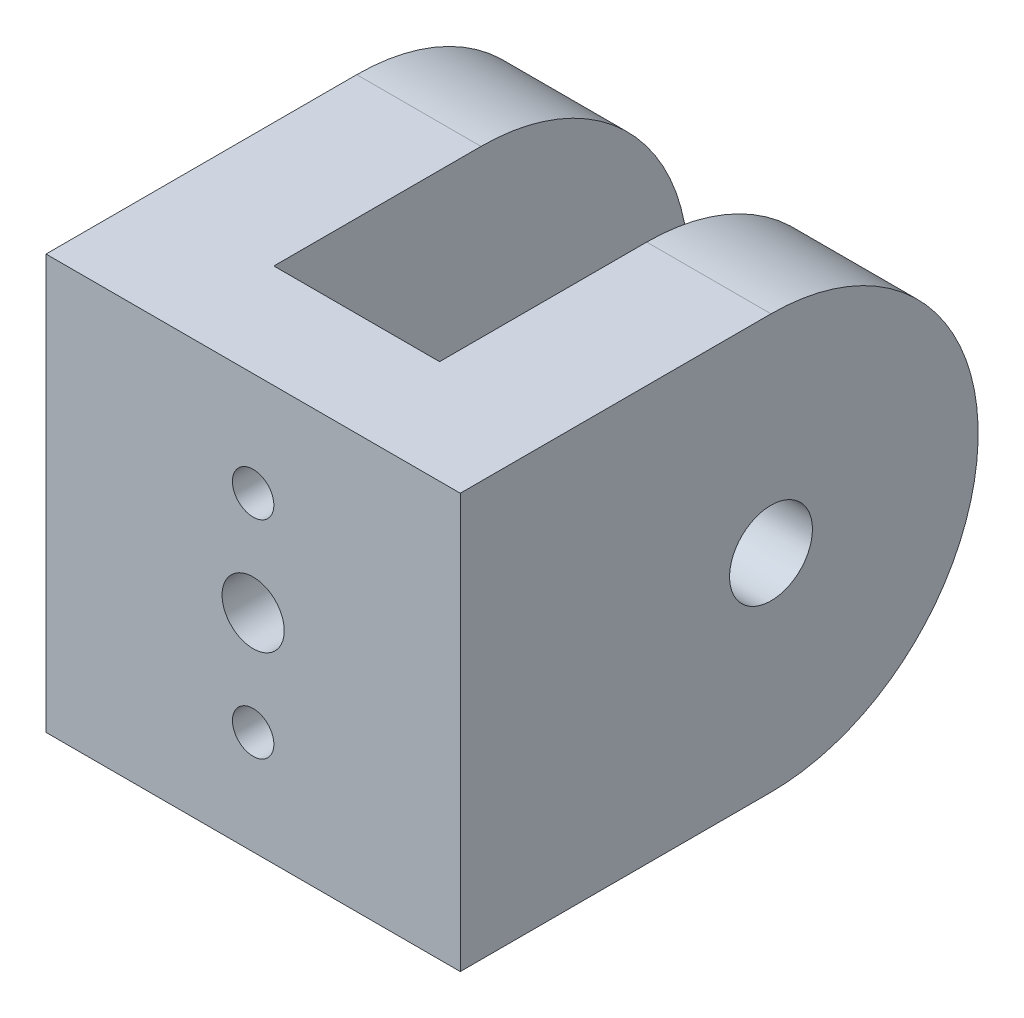
SolidWorks part; units mm, degrees
ref_plane "Front" through (0, 0, 0) normal (0, 0, 1) x (1, 0, 0)
ref_plane "Top" through (0, 0, 0) normal (0, 1, 0) x (1, 0, 0)
ref_plane "Right" through (0, 0, 0) normal (1, 0, 0) x (0, 0, -1)
sketch "Sketch1" plane through (0, 0, 0) normal (0, 0, 1) x (1, 0, 0)
  line L1 (0, 0) -> (80, 0)
  line L2 (0, 0) -> (0, 80)
  line L3 (0, 80) -> (80, 80)
  line L4 (80, 0) -> (80, 80)
  dimension "D1" = 80
  dimension "D2" = 80
extrude "Boss-Extrude1" add sketch "Sketch1" along normal blind 2
sketch "Sketch2" plane through (0, 0, 2) normal (0, 0, 1) x (1, 0, 0)
  line L0 (1, 79) -> (1, 1)
  line L1 (0, 80) -> (80, 80)
  line L2 (0, 80) -> (0, 0)
  line L3 (0, 0) -> (80, 0)
  line L4 (80, 80) -> (80, 0)
  line L5 (1, 1) -> (79, 1)
  line L6 (79, 79) -> (79, 1)
  line L7 (1, 79) -> (79, 79)
  dimension "D1" = 1
extrude "Boss-Extrude2" add sketch "Sketch2" along normal blind 15
fillet "Fillet1" radius 20 4 edges at (79, 1, 9.5) (1, 1, 9.5) (79, 79, 9.5) (1, 79, 9.5)
fillet "Fillet2" radius 10 8 edges at (73.1421, 73.1421, 2) (79, 40, 2) (73.1421, 6.8579, 2) (40, 1, 2) (6.8579, 6.8579, 2) (1, 40, 2) (6.8579, 73.1421, 2) (40, 79, 2)
fillet "Fillet3" radius 20 4 edges at (80, 0, 8.5) (80, 80, 8.5) (0, 80, 8.5) (0, 0, 8.5)
fillet "Fillet4" radius 10 8 edges at (5.8579, 5.8579, 0) (0, 40, 0) (5.8579, 74.1421, 0) (40, 80, 0) (74.1421, 74.1421, 0) (80, 40, 0) (74.1421, 5.8579, 0) (40, 0, 0)
sketch "Sketch3" plane through (0, 0, 17) normal (0, 0, 1) x (1, 0, 0)
  line L0 (72.2928, 5.3721) -> (70.635, 4.1054)
  line L1 (11, 40) -> (54.2273, 40)
  line L2 (11, 59) -> (11, 21) construction
  line L3 (40, 11) -> (40, 48.3049)
  line L4 (21, 11) -> (59, 11) construction
  line L5 (9.365, 4.1054) -> (9.365, 7.565)
  line L6 (7.565, 9.365) -> (3.996, 9.365)
  line L7 (3.996, 9.365) -> (7.7072, 5.3721)
  line L8 (7.7072, 5.3721) -> (9.365, 4.1054)
  line L9 (76.004, 9.365) -> (72.2928, 5.3721)
  line L10 (72.435, 9.365) -> (76.004, 9.365)
  line L11 (70.635, 4.1054) -> (70.635, 7.565)
  line L12 (70.635, 75.8946) -> (70.635, 72.435)
  line L13 (72.435, 70.635) -> (76.004, 70.635)
  line L14 (76.004, 70.635) -> (72.2928, 74.6279)
  line L15 (7.7072, 74.6279) -> (9.365, 75.8946)
  line L16 (3.996, 70.635) -> (7.7072, 74.6279)
  line L17 (7.565, 70.635) -> (3.996, 70.635)
  line L18 (9.365, 75.8946) -> (9.365, 72.435)
  line L19 (72.2928, 74.6279) -> (70.635, 75.8946)
  circle A0 centre (7.565, 7.565) radius 1
  arc A1 (1, 21) -> (21, 1) centre (21, 21) ccw construction
  arc A2 (9.365, 7.565) -> (7.565, 9.365) centre (7.565, 7.565) ccw
  arc A3 (70.635, 7.565) -> (72.435, 9.365) centre (72.435, 7.565) cw
  circle A4 centre (72.435, 7.565) radius 1
  circle A5 centre (72.435, 72.435) radius 1
  arc A6 (70.635, 72.435) -> (72.435, 70.635) centre (72.435, 72.435) ccw
  arc A7 (9.365, 72.435) -> (7.565, 70.635) centre (7.565, 72.435) cw
  circle A8 centre (7.565, 72.435) radius 1
  arc M13 (1, 59) -> (21, 79) centre (21, 59) cw
  arc M15 (59, 79) -> (79, 59) centre (59, 59) cw
  arc M17 (79, 21) -> (59, 1) centre (59, 21) cw
  arc M19 (21, 1) -> (1, 21) centre (21, 21) cw
  dimension "D1" = 2
  dimension "D3" = 0.8
extrude "Boss-Extrude3" add sketch "Sketch3" against normal blind 6 contours A4 L10 A3 L11 M17 | L11 L0 L9 L10 M17 | L5 A2 L6 A0 M19 | L7 L8 L5 L6 M19 | A8 L17 A7 L18 M13 | L18 L15 L16 L17 M13 | L12 A6 L13 A5 M15 | L14 L19 L12 L13 M15
sketch "Sketch4" plane through (0, 0, 0) normal (0, 0, -1) x (-1, 0, 0)
  line L0 (-40, 10) -> (-40, 61.2218)
  line L1 (-60, 10) -> (-20, 10) construction
  line L2 (-70, 40) -> (-30, 40)
  line L3 (-70, 60) -> (-70, 20) construction
  line L5 (-30, 30) -> (-50, 30)
  line L6 (-30, 30) -> (-30, 50)
  line L7 (-30, 50) -> (-50, 50)
  line L8 (-50, 30) -> (-50, 50)
  point P12 (-60.0695, 29.8786)
  point P13 (-40, 30)
  point P14 (-50, 40)
  dimension "D1" = 20
  dimension "D2" = 20
extrude "Boss-Extrude4" add sketch "Sketch4" along normal blind 5 contours L5 L6 L2 L0 | L6 L7 L0 L2 | L8 L2 L0 L7 | L8 L5 L0 L2
sketch "Sketch5" plane through (0, 0, -5) normal (0, 0, -1) x (-1, 0, 0)
  line L0 (-30, 50) -> (-50, 50) construction
  line L1 (-30, 30) -> (-36, 30)
  line L2 (-30, 30) -> (-30, 50)
  line L3 (-30, 50) -> (-36, 50)
  line L4 (-36, 30) -> (-36, 50)
  line L6 (-44, 50) -> (-50, 50)
  line L7 (-44, 50) -> (-44, 30)
  line L8 (-44, 30) -> (-50, 30)
  line L9 (-50, 50) -> (-50, 30)
  dimension "D1" = 6
  dimension "D2" = 6
extrude "Boss-Extrude5" add sketch "Sketch5" along normal blind 20
sketch "Sketch6" plane through (30, 0, 0) normal (-1, 0, 0) x (0, 0, 1)
  line L0 (-25, 30) -> (-25, 50) construction
  line L1 (-25, 50) -> (0, 50) construction
  line L2 (-25, 30) -> (0, 30) construction
  line L3 (-15, 30) -> (-19.7567, 21.1862)
  line L4 (-19.7567, 21.1862) -> (-29.1684, 27.648)
  line L5 (-29.1684, 27.648) -> (-29.1684, 53.8462)
  line L6 (-29.1684, 53.8462) -> (-15, 50)
  arc A0 (-15, 50) -> (-15, 30) centre (-15, 40) ccw
extrude "Cut-Extrude1" cut sketch "Sketch6" against normal blind 23
sketch "Sketch7" plane through (30, 0, 0) normal (-1, 0, 0) x (0, 0, 1)
  circle A1 centre (-15, 40) radius 2
  dimension "D1" = 4
extrude "Cut-Extrude2" cut sketch "Sketch7" against normal blind 23
sketch "Sketch8" plane through (30, 0, 0) normal (-1, 0, 0) x (0, 0, 1)
  circle A0 centre (-15, 40) radius 3.5
  dimension "D1" = 7
extrude "Cut-Extrude3" cut sketch "Sketch8" against normal blind 3
sketch "Sketch9" plane through (0, 0, -5) normal (0, 0, -1) x (-1, 0, 0)
  line L0 (-36, 30) -> (-44, 30) construction
  line L1 (-30, 50) -> (-50, 50) construction
  circle A0 centre (-40, 45) radius 1
  circle A1 centre (-40, 35) radius 1
  point P6 (-40, 30)
  point P10 (-40, 50)
  dimension "D3" = 2
  dimension "D4" = 2
  dimension "D1" = 5
  dimension "D2" = 5
extrude "Cut-Extrude4" cut sketch "Sketch9" against normal blind 18
sketch "Sketch10" plane through (0, 0, -5) normal (0, 0, -1) x (-1, 0, 0)
  line L0 (-30, 50) -> (-50, 50) construction
  line L1 (-50, 50) -> (-50, 30) construction
  circle A0 centre (-40, 40) radius 1.5
  point P2 (0, 0)
  point P5 (-40, 50)
  point P8 (0, 0)
  point P9 (-50, 40)
  dimension "D1" = 3
extrude "Cut-Extrude5" cut sketch "Sketch10" against normal blind 18
sketch "Sketch11" plane through (0, 0, 0) normal (0, 0, -1) x (-1, 0, 0)
  circle A0 centre (-39.6548, 38.6565) radius 69.2834
extrude "Cut-Extrude6" cut sketch "Sketch11" against normal blind 37
